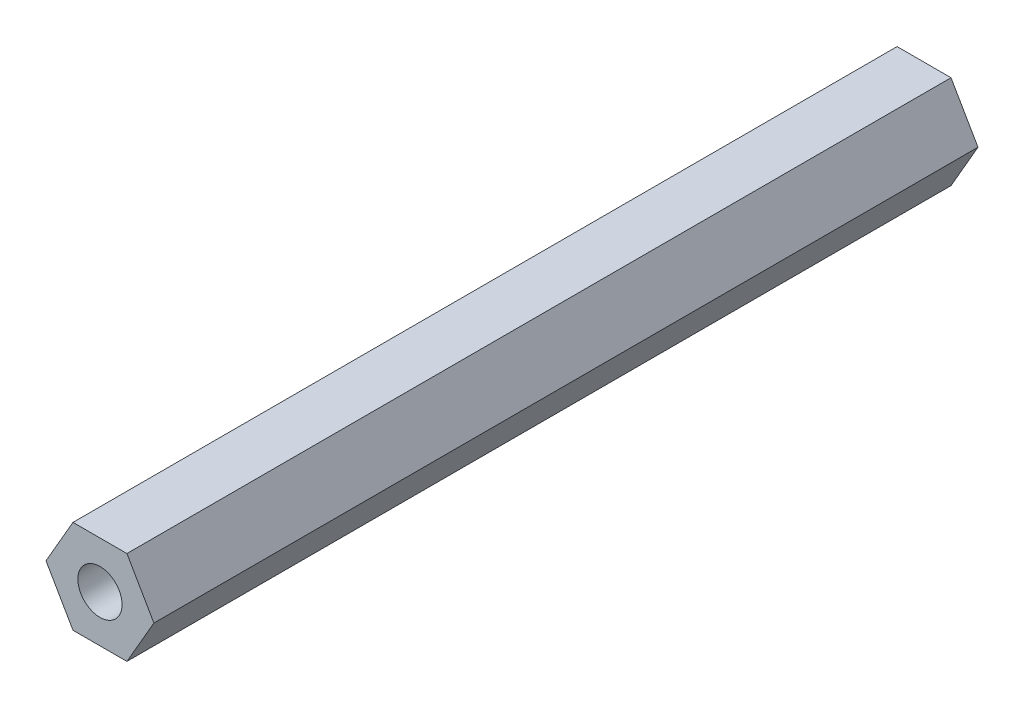
SolidWorks part; units mm, degrees
ref_plane "Alzado" through (0, 0, 0) normal (0, 0, 1) x (1, 0, 0)
ref_plane "Planta" through (0, 0, 0) normal (0, 1, 0) x (1, 0, 0)
ref_plane "Vista lateral" through (0, 0, 0) normal (1, 0, 0) x (0, 0, -1)
sketch "Croquis1" plane through (0, 0, 0) normal (0, 0, 1) x (1, 0, 0)
  line L1 (3.6662, 0) -> (1.8331, 3.175)
  line L2 (1.8331, 3.175) -> (-1.8331, 3.175)
  line L3 (-1.8331, 3.175) -> (-3.6662, 0)
  line L4 (-3.6662, 0) -> (-1.8331, -3.175)
  line L5 (-1.8331, -3.175) -> (1.8331, -3.175)
  line L6 (1.8331, -3.175) -> (3.6662, 0)
  circle A0 centre (0, 0) radius 3.175 construction
  circle A1 centre (0, 0) radius 1.5
  dimension "D1" = 6.35
  dimension "D2" = 3
extrude "Saliente-Extruir1" add sketch "Croquis1" along normal blind 56
